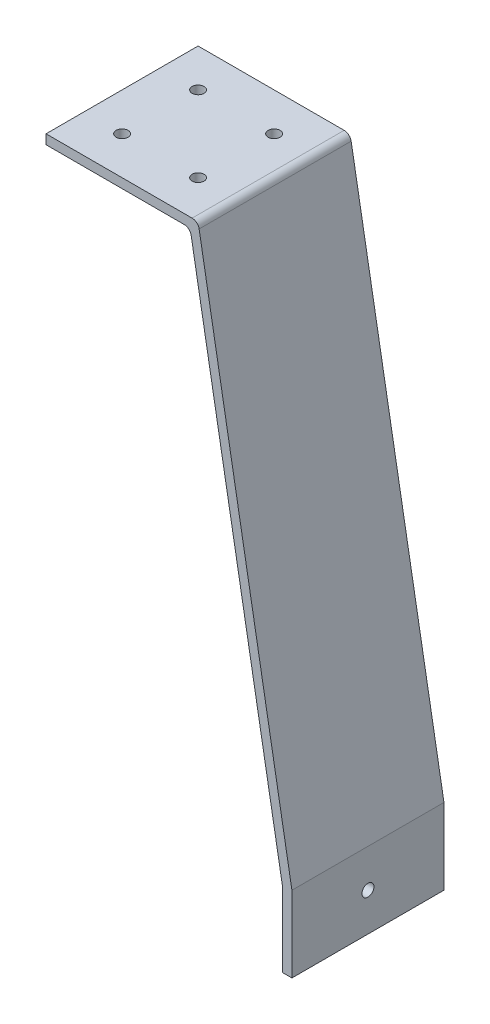
SolidWorks part; units mm, degrees
ref_plane "Front Plane" through (0, 0, 0) normal (0, 0, 1) x (1, 0, 0)
ref_plane "Top Plane" through (0, 0, 0) normal (0, 1, 0) x (1, 0, 0)
ref_plane "Right Plane" through (0, 0, 0) normal (1, 0, 0) x (0, 0, -1)
sketch "Sketch1" plane through (0, 0, 0) normal (0, 0, 1) x (1, 0, 0)
  line L0 (0, 0) -> (50.8, 0)
  line L1 (50.8, 0) -> (82.1509, -177.8)
  line L2 (82.1509, -177.8) -> (82.1509, -203.2)
  line L3 (82.1509, -203.2) -> (78.9759, -203.2)
  line L4 (78.9759, -203.2) -> (78.9759, -178.0778)
  line L5 (78.9759, -178.0778) -> (48.1359, -3.175)
  line L6 (48.1359, -3.175) -> (0, -3.175)
  line L7 (0, -3.175) -> (0, 0)
  line L8 (50.8, 0) -> (50.8, -53.1995) construction
  dimension "D1" = 10
  dimension "D2" = 3.175
  dimension "D3" = 3.175
  dimension "D4" = 3.175
  dimension "D5" = 203.2
  dimension "D6" = 50.8
  dimension "D7" = 25.4
extrude "Boss-Extrude1" add sketch "Sketch1" along normal mid plane 50.8
sketch "Sketch3" plane through (0, 0, 0) normal (0, 1, 0) x (1, 0, 0)
  line L0 (25.4, 12.7) -> (25.4, 25.4) construction
  line L1 (12.7, -12.7) -> (38.1, -12.7) construction
  line L2 (12.7, -12.7) -> (12.7, 12.7) construction
  line L3 (12.7, 12.7) -> (38.1, 12.7) construction
  line L4 (50.8, 25.4) -> (0, 25.4)
  line L5 (0, 25.4) -> (0, -25.4)
  line L6 (0, -25.4) -> (50.8, -25.4)
  line L7 (50.8, -25.4) -> (50.8, 25.4)
  line L8 (50.8, 25.4) -> (0, 25.4) construction
  line L9 (0, 25.4) -> (0, -25.4) construction
  line L10 (0, -25.4) -> (50.8, -25.4) construction
  line L11 (50.8, -25.4) -> (50.8, 25.4) construction
  line L12 (38.1, -12.7) -> (38.1, 12.7) construction
  line L13 (12.7, 0) -> (0, 0) construction
  line L14 (38.1, 0) -> (50.8, 0) construction
  line L15 (25.4, -12.7) -> (25.4, -25.4) construction
  circle A0 centre (12.7, -12.7) radius 2
  circle A1 centre (12.7, 12.7) radius 2
  circle A2 centre (38.1, 12.7) radius 2
  circle A3 centre (38.1, -12.7) radius 2
  dimension "D3" = 4
  dimension "D2" = 12.7
  dimension "D1" = 0
extrude "Cut-Extrude1" cut sketch "Sketch3" against normal blind 50.8
sketch "Sketch4" plane through (82.1509, 0, 0) normal (1, 0, 0) x (0, 0, -1)
  line L0 (0, -177.8) -> (0, -203.2) construction
  line L1 (-25.4, -190.5) -> (25.4, -190.5) construction
  line L4 (25.4, -203.2) -> (25.4, -177.8)
  line L5 (25.4, -177.8) -> (-25.4, -177.8)
  line L6 (-25.4, -177.8) -> (-25.4, -203.2)
  line L7 (-25.4, -203.2) -> (25.4, -203.2)
  line L8 (25.4, -203.2) -> (25.4, -177.8) construction
  line L9 (25.4, -177.8) -> (-25.4, -177.8) construction
  line L10 (-25.4, -177.8) -> (-25.4, -203.2) construction
  line L11 (-25.4, -203.2) -> (25.4, -203.2) construction
  circle A0 centre (0, -190.5) radius 2
  dimension "D2" = 4
  dimension "D1" = 0
extrude "Cut-Extrude2" cut sketch "Sketch4" against normal through all
fillet "Fillet1" radius 2.38 2 edges at (50.8, 0, 0) (48.1359, -3.175, 0)
